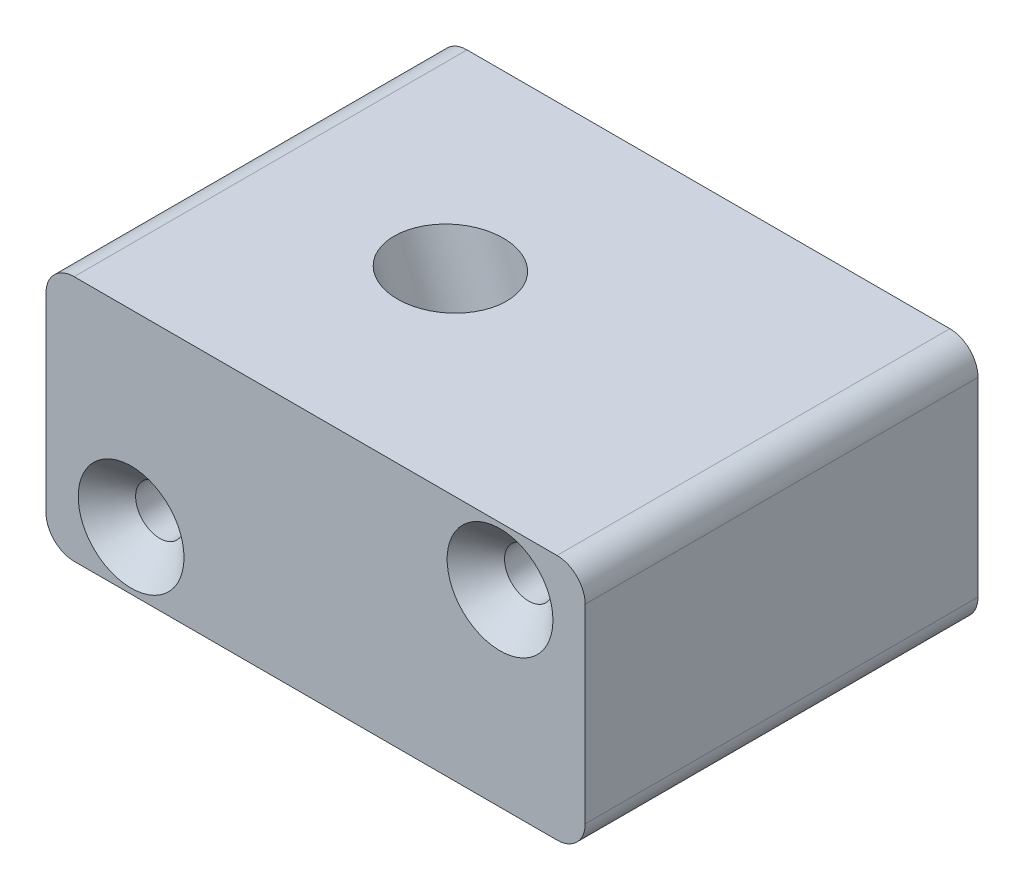
SolidWorks part; units mm, degrees
material "6061 Alloy"
ref_plane "Top Plane" through (0, 0, 0) normal (0, 0, 1) x (1, 0, 0)
ref_plane "Front Plane" through (0, 0, 0) normal (0, 1, 0) x (1, 0, 0)
ref_plane "Right Plane" through (0, 0, 0) normal (1, 0, 0) x (0, 0, -1)
sketch "Sketch1" plane through (0, 0, 0) normal (0, 0, 1) x (1, 0, 0)
  line L1 (-21.45, -10.95) -> (21.45, -10.95)
  line L2 (-23.95, -8.45) -> (-23.95, 8.45)
  line L3 (-21.45, 10.95) -> (21.45, 10.95)
  line L4 (23.95, -8.45) -> (23.95, 8.45)
  line L5 (-23.95, -10.95) -> (23.95, 10.95) construction
  line L6 (-23.95, 10.95) -> (23.95, -10.95) construction
  arc A0 (-23.95, -8.45) -> (-21.45, -10.95) centre (-21.45, -8.45) ccw
  arc A1 (21.45, -10.95) -> (23.95, -8.45) centre (21.45, -8.45) ccw
  arc A2 (23.95, 8.45) -> (21.45, 10.95) centre (21.45, 8.45) ccw
  arc A3 (-21.45, 10.95) -> (-23.95, 8.45) centre (-21.45, 8.45) ccw
  point P0 (0, 0)
  dimension "D3" = 2.5
  dimension "D1" = 47.9
  dimension "D2" = 21.9
extrude "Boss-Extrude1" add sketch "Sketch1" along normal mid plane 34.9
sketch "Sketch11" plane through (0, 0, 0) normal (0, 0, 1) x (1, 0, 0)
  line L0 (-3.8776, 10.95) -> (3.8555, -10.95)
  line L1 (21.45, 10.95) -> (-21.45, 10.95) construction
  line L2 (0, 10.95) -> (0, -10.95) construction
  line L3 (-21.45, -10.95) -> (21.45, -10.95) construction
sketch "Sketch12" plane through (0, 10.95, 0) normal (0, 1, 0) x (1, 0, 0)
  line L0 (-3.8776, 0) -> (3.8555, 0) construction
  circle A0 centre (-3.0877, 0) radius 4.7714
  dimension "D1" = 9.5428
sweep "Cut-Sweep1" [suppressed] cut profiles "Sketch12" path "Sketch11"
sketch "Sketch15" plane through (0, 0, 17.45) normal (0, 0, 1) x (1, 0, 0)
  line L0 (-23.95, -8.45) -> (23.95, 8.45) construction
  line L9 (-21.45, -10.95) -> (0, 10.95) construction
  line L10 (21.45, 10.95) -> (-21.45, 10.95) construction
  line L12 (21.45, 10.95) -> (0, -10.95) construction
  line L13 (-21.45, -10.95) -> (21.45, -10.95) construction
  point P0 (-16.3883, -5.7821)
  point P2 (16.3883, 5.7821)
hole_wizard "CSK for M4 Flat Head Machine Screw1" positions "Sketch15" profile "Sketch14" countersink size "M4" standard "ANSI Metric" end condition through all
sketch "Sketch14" plane through (-16.3883, -5.7821, 17.45) normal (1, 0, 0) x (0, -1, 0)
  line L0 (0, 0) -> (0, 34.9)
  line L1 (0, 34.9) -> (2.15, 34.9)
  line L2 (2.15, 34.9) -> (2.15, 2.55)
  line L3 (2.15, 2.55) -> (4.7, 0)
  line L5 (4.7, 0) -> (0, 0)
  line L6 (-2.15, 2.55) -> (-4.7, 0) construction
  line L11 (0, -6.35) -> (0, 107.95) construction
  dimension "Thru Hole Dia." = 4.3
  dimension "Thru Hole Depth" = 34.9
  dimension "Near C'Sink Dia." = 9.4
  dimension "Near C'Sink Angle" = 90
ref_plane "Lie Angle Plane" through (-2.7158, -0.9885, 0) normal (0.9397, 0.342, 0) x (0, 0, -1)
sketch "Sketch21" [suppressed] plane through (-2.7626, -0.8976, 0) normal (0.9511, 0.309, 0) x (0, 0, -1)
  line L2 (-2.1354, -40.7451) -> (0, 0)
  line L3 (0, 0) -> (1.9625, 37.4468)
  line L4 (-2.1354, -40.7451) -> (2.0556, -40.9647)
  line L5 (2.0556, -40.9647) -> (6.1648, 37.4419)
  line L6 (1.9625, 37.4468) -> (6.1648, 37.4419)
  point P2 (0, 0)
  dimension "D1" = 4.191
revolve "Cut-Revolve1" [suppressed] cut sketch "Sketch21" angle 360 about L3
ref_plane "Lie Angle offset" through (-1.2123, -0.4412, 0) normal (0.9397, 0.342, 0) x (0, 0, -1)
sketch "Sketch24" plane through (-1.2123, -0.4412, 0) normal (0.9397, 0.342, 0) x (0, 0, -1)
  line L4 (-0.115, 19.5553) -> (-0.115, -21.8488)
  line L5 (-0.115, -21.8488) -> (4.584, -21.8488)
  line L6 (4.584, -21.8488) -> (4.584, 19.5553)
  line L7 (4.584, 19.5553) -> (-0.115, 19.5553)
  line L8 (-17.45, 2.9533) -> (-17.45, 17.626) construction
  line L9 (-17.45, 2.9533) -> (17.45, 2.9533) construction
  dimension "D1" = 4.699
  dimension "D2" = 17.335
  dimension "D3" = 16.602
revolve "Hosel Diameter" cut sketch "Sketch24" angle 360 about L4
